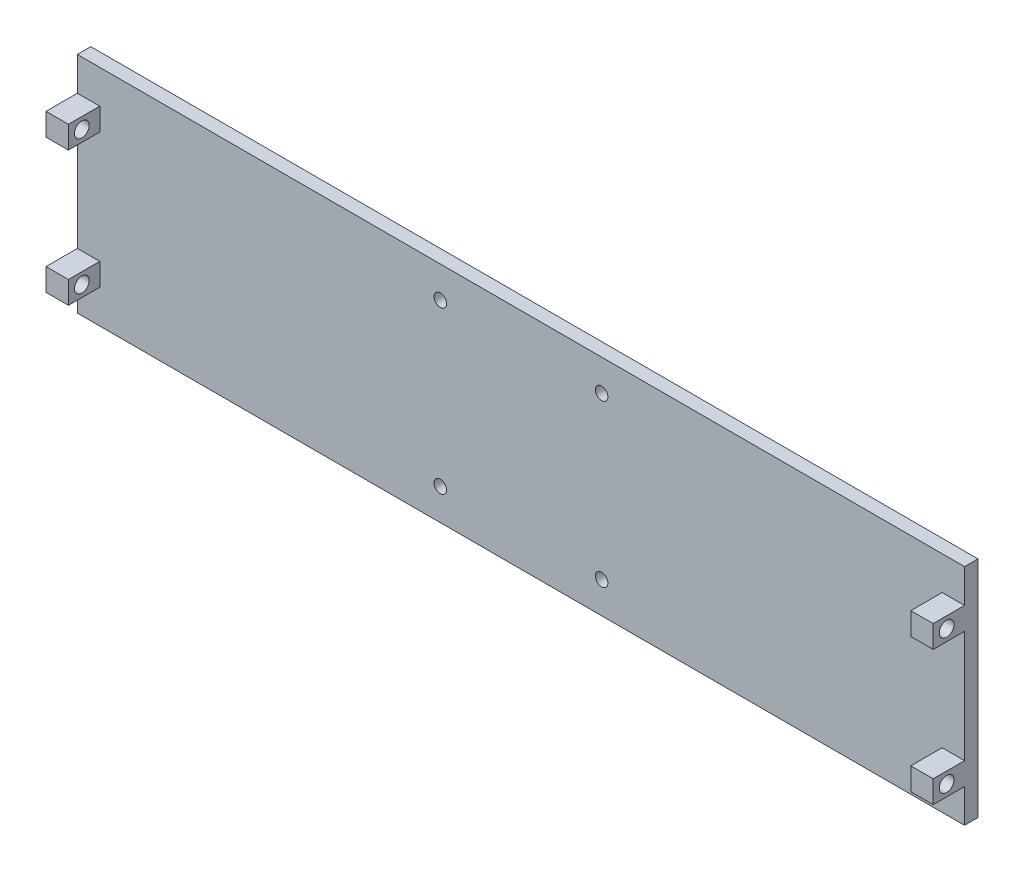
SolidWorks part; units mm, degrees
ref_plane "前视基准面" through (0, 0, 0) normal (0, 0, 1) x (1, 0, 0)
ref_plane "上视基准面" through (0, 0, 0) normal (0, 1, 0) x (1, 0, 0)
ref_plane "右视基准面" through (0, 0, 0) normal (1, 0, 0) x (0, 0, -1)
sketch "草图1" plane through (0, 0, 0) normal (0, 0, 1) x (1, 0, 0)
  line L1 (-99, -25) -> (99, -25)
  line L2 (-99, -25) -> (-99, 25)
  line L3 (-99, 25) -> (99, 25)
  line L4 (99, -25) -> (99, 25)
  line L5 (-99, -25) -> (99, 25) construction
  line L6 (-99, 25) -> (99, -25) construction
  point P0 (0, 0)
  dimension "D1" = 50
  dimension "D2" = 198
extrude "凸台-拉伸1" add sketch "草图1" along normal blind 3
sketch "草图4" plane through (-99, 0, 0) normal (-1, 0, 0) x (0, 0, 1)
  line L0 (0, 0) -> (0, -15)
  line L2 (0, 25) -> (0, -25) construction
  line L3 (0, 0) -> (0, 15)
  line L4 (0, 15) -> (5, 15)
  line L5 (0, -15) -> (5, -15)
  line L6 (0, -15) -> (7, -15)
  line L7 (0, 12.5) -> (10, 12.5)
  line L8 (0, 12.5) -> (0, 17.5)
  line L9 (0, 17.5) -> (10, 17.5)
  line L10 (10, 12.5) -> (10, 17.5)
  line L11 (0, 12.5) -> (10, 17.5) construction
  line L12 (0, 17.5) -> (10, 12.5) construction
  line L13 (0, -17.5) -> (10, -17.5)
  line L14 (0, -17.5) -> (0, -12.5)
  line L15 (0, -12.5) -> (10, -12.5)
  line L16 (10, -17.5) -> (10, -12.5)
  line L17 (0, -17.5) -> (10, -12.5) construction
  line L18 (0, -12.5) -> (10, -17.5) construction
  line L19 (0, 15) -> (7, 15)
  circle A0 centre (7, 15) radius 1.65
  circle A1 centre (7, -15) radius 1.65
  dimension "D11" = 3.3
  dimension "D12" = 3.3
  dimension "D1" = 15
  dimension "D2" = 15
  dimension "D3" = 5
  dimension "D4" = 5
  dimension "D5" = 10
  dimension "D6" = 5
  dimension "D7" = 10
  dimension "D8" = 5
  dimension "D9" = 7
  dimension "D10" = 7
extrude "凸台-拉伸2" add sketch "草图4" against normal blind 5
sketch "草图5" plane through (99, 0, 0) normal (1, 0, 0) x (0, 0, -1)
  line L0 (0, 0) -> (0, 15)
  line L1 (0, -25) -> (0, 25) construction
  line L2 (0, 0) -> (0, -15)
  line L3 (0, 15) -> (-5, 15)
  line L4 (0, -15) -> (-5, -15)
  line L5 (0, 15) -> (-7, 15)
  line L6 (0, 12.5) -> (-10, 12.5)
  line L7 (0, 12.5) -> (0, 17.5)
  line L8 (0, 17.5) -> (-10, 17.5)
  line L9 (-10, 12.5) -> (-10, 17.5)
  line L10 (0, 12.5) -> (-10, 17.5) construction
  line L11 (0, 17.5) -> (-10, 12.5) construction
  line L12 (-10, -17.5) -> (0, -17.5)
  line L13 (-10, -17.5) -> (-10, -12.5)
  line L14 (-10, -12.5) -> (0, -12.5)
  line L15 (0, -17.5) -> (0, -12.5)
  line L16 (-10, -17.5) -> (0, -12.5) construction
  line L17 (-10, -12.5) -> (0, -17.5) construction
  line L18 (0, -15) -> (-7, -15)
  circle A0 centre (-7, 15) radius 1.65
  circle A1 centre (-7, -15) radius 1.65
  dimension "D11" = 3.3
  dimension "D12" = 3.3
  dimension "D1" = 15
  dimension "D2" = 15
  dimension "D3" = 5
  dimension "D4" = 5
  dimension "D5" = 10
  dimension "D6" = 5
  dimension "D7" = 5
  dimension "D8" = 10
  dimension "D9" = 7
  dimension "D10" = 7
extrude "凸台-拉伸3" add sketch "草图5" against normal blind 5
sketch "草图6" plane through (0, 0, 3) normal (0, 0, 1) x (1, 0, 0)
  line L1 (-18, -18) -> (18, -18)
  line L2 (-18, -18) -> (-18, 18)
  line L3 (-18, 18) -> (18, 18)
  line L4 (18, -18) -> (18, 18)
  line L5 (-18, -18) -> (18, 18) construction
  line L6 (-18, 18) -> (18, -18) construction
  circle A0 centre (-18, 18) radius 1.4
  circle A1 centre (18, 18) radius 1.4
  circle A2 centre (18, -18) radius 1.4
  circle A3 centre (-18, -18) radius 1.4
  point P0 (0, 0)
  point P16 (0, 0)
  dimension "D3" = 2.8
  dimension "D1" = 36
  dimension "D2" = 36
  dimension "D4" = 4
extrude "切除-拉伸3" cut sketch "草图6" against normal blind 3 contours A0 | A3 | A2 | A1
